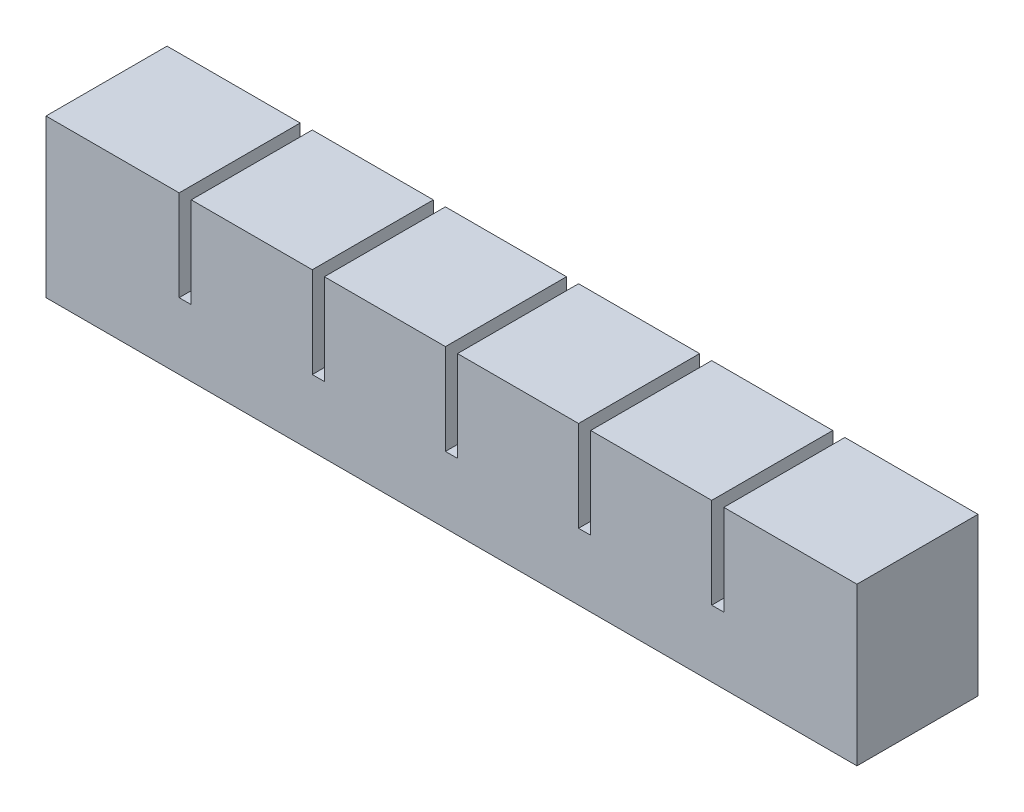
SolidWorks part; units mm, degrees
ref_plane "Front Plane" through (0, 0, 0) normal (0, 0, 1) x (1, 0, 0)
ref_plane "Top Plane" through (0, 0, 0) normal (0, 1, 0) x (1, 0, 0)
ref_plane "Right Plane" through (0, 0, 0) normal (1, 0, 0) x (0, 0, -1)
sketch "Sketch1" plane through (0, 0, 0) normal (0, 0, 1) x (1, 0, 0)
  line L1 (0, 0) -> (20, 0)
  line L2 (0, 0) -> (0, 20)
  line L3 (0, 20) -> (20, 20)
  line L4 (20, 0) -> (20, 20)
  dimension "D1" = 20
  dimension "D2" = 20
extrude "Boss-Extrude1" add sketch "Sketch1" along normal blind 20
sketch "Sketch2" plane through (0, 0, 0) normal (0, -1, 0) x (-1, 0, 0)
  line L0 (-20, -20) -> (-20, 0) construction
  line L1 (-5, -5) -> (-15, -5)
  line L2 (-5, -5) -> (-5, -15)
  line L3 (-5, -15) -> (-15, -15)
  line L4 (-15, -5) -> (-15, -15)
  line L5 (0, -20) -> (-20, -20) construction
  line L6 (0, -20) -> (0, 0) construction
  line L7 (0, 0) -> (-20, 0) construction
  dimension "D1" = 5
  dimension "D2" = 5
  dimension "D3" = 5
  dimension "D4" = 5
extrude "Cut-Extrude1" cut sketch "Sketch2" against normal blind 15
sketch "Sketch3" plane through (20, 0, 0) normal (1, 0, 0) x (0, 0, -1)
  line L0 (0, 0) -> (0, 20) construction
  line L1 (-20, 0) -> (0, 0)
  line L2 (-20, 0) -> (-20, 5)
  line L3 (-20, 5) -> (0, 5)
  line L4 (0, 0) -> (0, 5)
  dimension "D1" = 5
extrude "Boss-Extrude2" add sketch "Sketch3" along normal blind 2
pattern_linear "LPattern1" count 6 spacing 22 along (1, 0, 0) of bodies 103
combine bodies "Combine1" operation type add bodies to combine 104 105 106 103 107 108
sketch "Sketch4" plane through (130, 0, 0) normal (1, 0, 0) x (0, 0, -1)
  line L1 (-20, 20) -> (0, 20)
  line L2 (-20, 20) -> (-20, 5)
  line L3 (-20, 5) -> (0, 5)
  line L4 (0, 20) -> (0, 5)
extrude "Boss-Extrude3" add sketch "Sketch4" along normal up to surface (2 mm away) up to face at (132, 2.5, 10)
sketch "Sketch5" plane through (0, 0, 0) normal (-1, 0, 0) x (0, 0, 1)
  line L1 (0, 0) -> (20, 0)
  line L2 (0, 0) -> (0, 20)
  line L3 (0, 20) -> (20, 20)
  line L4 (20, 0) -> (20, 20)
extrude "Boss-Extrude5" add sketch "Sketch5" along normal blind 2
ref_point "Point1"
sketch "Sketch7" plane through (0, 0, 0) normal (0, -1, 0) x (-1, 0, 0)
  line L0 (-125, -5) -> (-125, -15) construction
  line L1 (-5, -9) -> (-125, -9)
  line L2 (-5, -9) -> (-5, -11)
  line L3 (-5, -11) -> (-125, -11)
  line L4 (-125, -9) -> (-125, -11)
  line L5 (-5, -9) -> (-125, -11) construction
  line L6 (-5, -11) -> (-125, -9) construction
  point P0 (-65, -10)
  dimension "D1" = 2
extrude "Cut-Extrude2" cut sketch "Sketch7" against normal blind 2
sketch "Sketch8" plane through (0, 0, 0) normal (0, -1, 0) x (1, 0, 0)
  line L1 (-2, 20) -> (132, 20)
  line L2 (-2, 20) -> (-2, 0)
  line L3 (-2, 0) -> (132, 0)
  line L4 (132, 20) -> (132, 0)
extrude "Boss-Extrude6" add sketch "Sketch8" along normal blind 6
